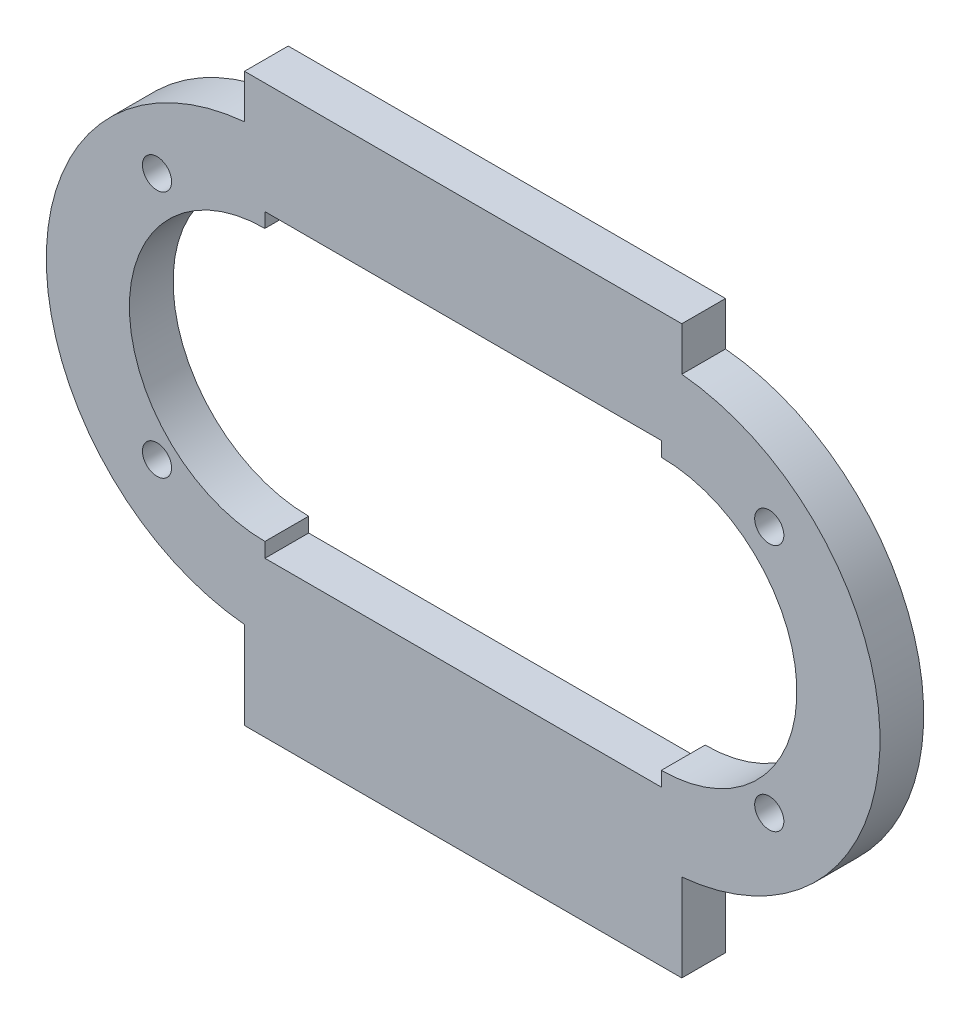
SolidWorks part; units mm, degrees
ref_plane "Alzado" through (0, 0, 0) normal (0, 0, 1) x (1, 0, 0)
ref_plane "Planta" through (0, 0, 0) normal (0, 1, 0) x (1, 0, 0)
ref_plane "Vista lateral" through (0, 0, 0) normal (1, 0, 0) x (0, 0, -1)
sketch "Croquis1" plane through (0, 0, 0) normal (0, 0, 1) x (1, 0, 0)
  line L0 (13.5968, 10.2975) -> (13.5968, -9.6326) construction
  line L1 (28.5968, -20.9342) -> (28.5968, -14.9342)
  line L2 (-1.4032, -20.9342) -> (-1.4032, -14.9342)
  line L3 (0, -10.2975) -> (27.1937, -10.2975)
  line L4 (0, 10.2975) -> (0, 9.2975)
  line L5 (-9.2975, 0) -> (36.2975, 0) construction
  line L6 (28.5968, 17.9342) -> (28.5968, 14.9342)
  line L7 (-1.4032, 17.9342) -> (28.5968, 17.9342)
  line L8 (0, 10.2975) -> (27.1937, 10.2975)
  line L9 (27.1937, 10.2975) -> (27.1937, 9.2975)
  line L10 (-1.4032, -20.9342) -> (28.5968, -20.9342)
  line L11 (27.1937, -9.2975) -> (27.1937, -10.2975)
  line L12 (0, -9.2975) -> (0, -10.2975)
  line L13 (-1.4032, 17.9342) -> (-1.4032, 14.9342)
  arc A0 (0, 9.2975) -> (0, -9.2975) centre (0, 0) ccw
  arc A1 (27.1937, 9.2975) -> (27.1937, -9.2975) centre (27.1937, 0) cw
  circle A4 centre (-7.4032, 8.8674) radius 1
  circle A5 centre (34.5968, 8.8674) radius 1
  circle A6 centre (34.5968, -8.1326) radius 1
  circle A7 centre (-7.4032, -8.1326) radius 1
  arc A8 (-1.4032, 14.9342) -> (-1.4032, -14.9342) centre (0, 0) ccw
  arc A9 (28.5968, 14.9342) -> (28.5968, -14.9342) centre (27.1937, 0) cw
  dimension "D1" = 9.2975
  dimension "D2" = 1
  dimension "D8" = 2
  dimension "D9" = 15
  dimension "D10" = 17
  dimension "D11" = 15
  dimension "D3" = 6
  dimension "D4" = 15
  dimension "D5" = 21
  dimension "D6" = 21
  dimension "D7" = 17
  dimension "D12" = 3
  dimension "D13" = 3
extrude "Saliente-Extruir1" add sketch "Croquis1" along normal blind 3
